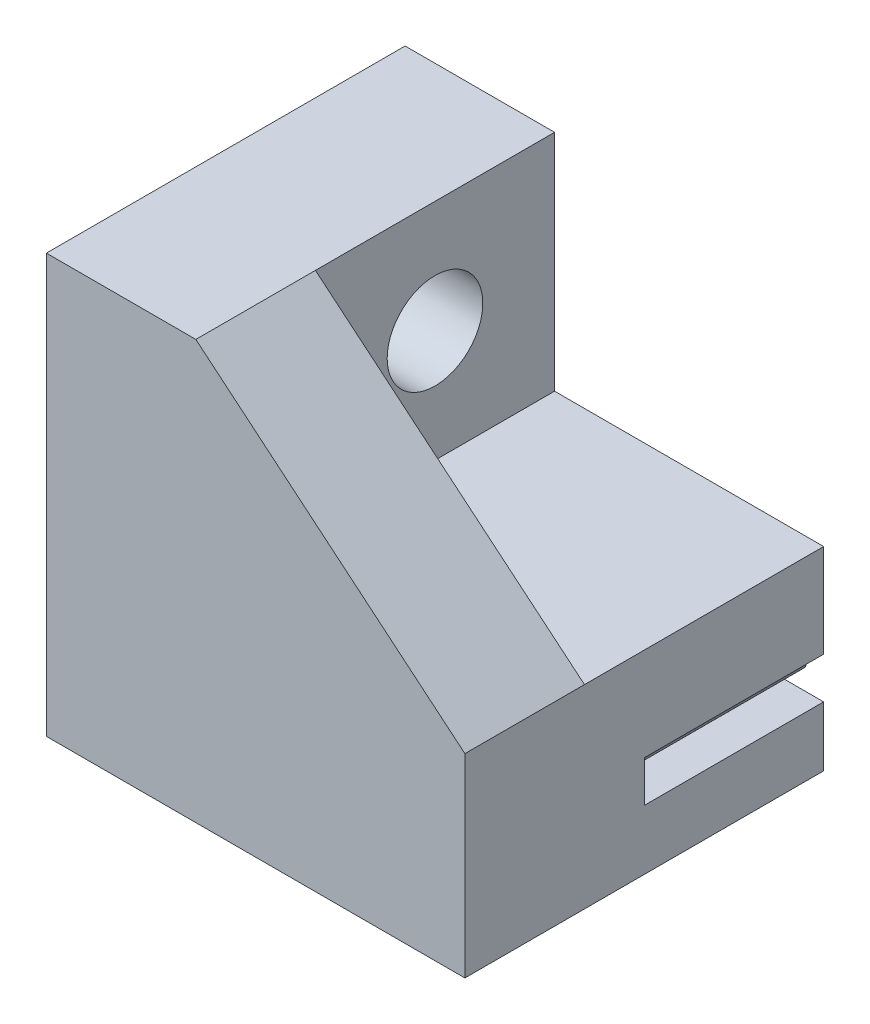
SolidWorks part; units mm, degrees
material "ABS"
ref_plane "Front Plane" through (0, 0, 0) normal (0, 0, 1) x (1, 0, 0)
ref_plane "Top Plane" through (0, 0, 0) normal (0, 1, 0) x (1, 0, 0)
ref_plane "Right Plane" through (0, 0, 0) normal (1, 0, 0) x (0, 0, -1)
sketch "Sketch3" plane through (0, 0, 0) normal (0, 0, 1) x (1, 0, 0)
  line L1 (0, -2) -> (14, -2)
  line L2 (0, -2) -> (0, 4.5)
  line L3 (0, 4.5) -> (14, 4.5)
  line L4 (14, -2) -> (14, 4.5)
  dimension "D1" = 14
  dimension "D2" = 6.5
  dimension "D3" = 2
extrude "Boss-Extrude2" add sketch "Sketch3" along normal blind 8
sketch "Sketch1" plane through (0, 0, 0) normal (0, 0, 1) x (1, 0, 0)
  line L4 (1, 0.63) -> (1, 1.38) construction
  line L5 (0.7402, 0.63) -> (1.2598, 0.63)
  line L6 (2, 1.38) -> (2, 0)
  line L9 (0, 1.38) -> (0, 0)
  line L10 (0, 0) -> (2, 0)
  arc A0 (1.2598, 0.63) -> (1.4085, 0.7604) centre (1.2598, 0.78) ccw
  arc A1 (1.4085, 0.7604) -> (1.5011, 1.0682) centre (2.4, 0.63) cw
  arc A2 (1.5011, 1.0682) -> (2, 1.38) centre (2, 0.825) cw
  arc A3 (0.4989, 1.0682) -> (0, 1.38) centre (0, 0.825) ccw
  arc A4 (0.5915, 0.7604) -> (0.4989, 1.0682) centre (-0.4, 0.63) ccw
  arc A5 (0.7402, 0.63) -> (0.5915, 0.7604) centre (0.7402, 0.78) cw
  dimension "D1" = 0.555
  dimension "D2" = 1
  dimension "D3" = 0.15
  dimension "D4" = 0.4
  dimension "D5" = 0.75
  dimension "D6" = 2
  dimension "D7" = 1.38
extrude "Cut-Extrude1" cut sketch "Sketch1" along normal blind 6
pattern_linear "LPattern2" count 7 spacing 2 along (1, 0, 0) of "Cut-Extrude1"
sketch "Sketch4" plane through (0, 0, 0) normal (-1, 0, 0) x (0, 0, 1)
  line L0 (0, 4.5) -> (0, 1.38) construction
  line L1 (0, 12) -> (8, 12)
  line L2 (0, 12) -> (0, 4.5)
  line L3 (0, 4.5) -> (8, 4.5)
  line L4 (8, 12) -> (8, 4.5)
  dimension "D1" = 7.5
  dimension "D2" = 8
extrude "Boss-Extrude3" add sketch "Sketch4" against normal blind 5
sketch "Sketch5" plane through (0, 0, 0) normal (-1, 0, 0) x (0, 0, 1)
  line L0 (4, 4.5) -> (4, 8.25) construction
  line L2 (4, 8.25) -> (0, 8.25) construction
  line L4 (4, 8.25) -> (8, 8.25) construction
  line L5 (1.25, 9.8377) -> (1.25, 6.6623)
  line L6 (1.25, 6.6623) -> (4, 5.0746)
  line L7 (4, 5.0746) -> (6.75, 6.6623)
  line L8 (6.75, 6.6623) -> (6.75, 9.8377)
  line L9 (6.75, 9.8377) -> (4, 11.4254)
  line L10 (4, 11.4254) -> (1.25, 9.8377)
  line L11 (8, 4.5) -> (8, 12) construction
  line L12 (4, 8.25) -> (4, 12) construction
  line L13 (8, 12) -> (0, 12) construction
  circle A0 centre (4, 8.25) radius 2.75 construction
  dimension "D1" = 3.75
  dimension "D2" = 5.5
extrude "Cut-Extrude2" cut sketch "Sketch5" against normal blind 2
sketch "Sketch6" plane through (2, 0, 0) normal (-1, 0, 0) x (0, 0, 1)
  line L0 (4, 11.4254) -> (4, 5.0746) construction
  circle A0 centre (4, 8.25) radius 1.6
  dimension "D1" = 3.2
extrude "Cut-Extrude3" cut sketch "Sketch6" against normal blind 10
sketch "Sketch7" plane through (0, 0, 8) normal (0, 0, 1) x (1, 0, 0)
  line L0 (14, -2) -> (14, 4.5)
  line L1 (14, -2) -> (14, 4.5) construction
  line L2 (14, 4.5) -> (5, 12)
  line L3 (5, 12) -> (0, 12)
  line L4 (0, 12) -> (0, -2)
  line L5 (0, -2) -> (14, -2)
extrude "Boss-Extrude4" add sketch "Sketch7" along normal blind 4
